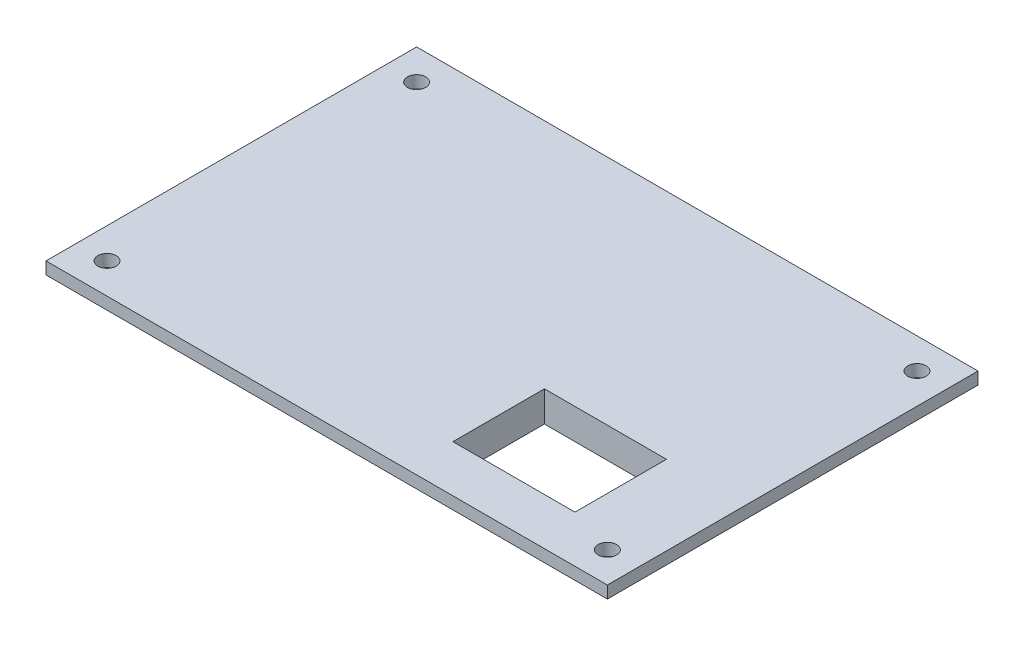
SolidWorks part; units mm, degrees
ref_plane "Спереди" through (0, 0, 0) normal (0, 0, 1) x (1, 0, 0)
ref_plane "Сверху" through (0, 0, 0) normal (0, 1, 0) x (1, 0, 0)
ref_plane "Справа" through (0, 0, 0) normal (1, 0, 0) x (0, 0, -1)
sketch "Эскиз1" plane through (0, 0, 0) normal (0, 1, 0) x (1, 0, 0)
  line L0 (-1000, 0) -> (49000, 0) construction
  line L1 (0, -1000) -> (0, 49000) construction
  line L2 (46, -1000) -> (46, 49000) construction
  line L3 (-46, -1000) -> (-46, 49000) construction
  line L4 (-1000, -30.37) -> (49000, -30.37) construction
  line L5 (-1000, 30.37) -> (49000, 30.37) construction
  line L6 (-46, 30.37) -> (-46, -30.37)
  line L7 (-46, -30.37) -> (46, -30.37)
  line L8 (46, -30.37) -> (46, 30.37)
  line L9 (46, 30.37) -> (-46, 30.37)
extrude "Бобышка-Вытянуть1" add sketch "Эскиз1" along normal blind 2
sketch "Эскиз2" plane through (0, 2, 0) normal (0, 1, 0) x (1, 0, 0)
  line L0 (-1000, 0) -> (49000, 0) construction
  line L1 (-41, -990.8865) -> (-41, 49009.1135) construction
  line L2 (41, -984.2014) -> (41, 49015.7986) construction
  line L3 (-1044.1748, 25.37) -> (48955.8252, 25.37) construction
  line L4 (42.5, -1000) -> (42.5, 49000) construction
  line L5 (-42.5, -1000) -> (-42.5, 49000) construction
  line L6 (-1038.32, -25.37) -> (48961.68, -25.37) construction
  line L7 (-1044.1748, 30.37) -> (48955.8252, 30.37) construction
  line L10 (-1038.32, -30.37) -> (48961.68, -30.37) construction
  line L12 (-46, -990.8865) -> (-46, 49009.1135) construction
  line L14 (46, -984.2014) -> (46, 49015.7986) construction
  circle A6 centre (-41, 25.37) radius 1.5
  circle A7 centre (41, 25.37) radius 1.5
  circle A8 centre (41, -25.37) radius 1.5
  circle A9 centre (-41, -25.37) radius 1.5
  dimension "D1" = 5
  dimension "D2" = 5
  dimension "D3" = 5
  dimension "D4" = 5
extrude "Вырез-Вытянуть1" cut sketch "Эскиз2" against normal blind 10
sketch "Эскиз3" plane through (0, 2, 0) normal (0, 1, 0) x (1, 0, 0)
  line L0 (-1033.1969, 30.37) -> (48966.8031, 30.37) construction
  line L2 (-1025.6477, -30.37) -> (48974.3523, -30.37) construction
  line L4 (-46, -985.3373) -> (-46, 49014.6627) construction
  line L6 (46, -986.4019) -> (46, 49013.5981) construction
  line L8 (0, -1000) -> (0, 49000) construction
  line L9 (-1000, 0) -> (49000, 0) construction
  line L14 (-1000, -15.185) -> (49000, -15.185) construction
  line L15 (23, -1000) -> (23, 49000) construction
  line L16 (33, -1000) -> (33, 49000) construction
  line L17 (13, -1000) -> (13, 49000) construction
  line L18 (76.37, 60.74) -> (-76.37, 60.74)
  line L19 (-76.37, 60.74) -> (-76.37, -60.74)
  line L20 (-76.37, -60.74) -> (76.37, -60.74)
  line L21 (76.37, -60.74) -> (76.37, 60.74)
  line L22 (76.37, 60.74) -> (-76.37, 60.74)
  line L23 (-76.37, 60.74) -> (-76.37, -60.74)
  line L24 (-76.37, -60.74) -> (76.37, -60.74)
  line L25 (76.37, -60.74) -> (76.37, 60.74)
  line L26 (-1000, -22.685) -> (49000, -22.685) construction
  line L27 (-1000, -7.685) -> (49000, -7.685) construction
  line L28 (13, -7.685) -> (13, -22.685)
  line L29 (13, -22.685) -> (33, -22.685)
  line L30 (33, -22.685) -> (33, -7.685)
  line L31 (33, -7.685) -> (13, -7.685)
  point P9 (23974.3523, -30.37)
  dimension "D1" = 30.37
extrude "Вырез-Вытянуть2" cut sketch "Эскиз3" against normal blind 10 contours L30 L31 L28 L29
sketch "Эскиз4" plane through (0, 0, 0) normal (0, -1, 0) x (1, 0, 0)
  line L0 (13, 22.685) -> (13, 7.685)
  line L1 (13, 7.685) -> (33, 7.685)
  line L2 (33, 7.685) -> (33, 22.685)
  line L3 (33, 22.685) -> (13, 22.685)
  line L4 (11, 24.685) -> (11, 5.685)
  line L5 (11, 5.685) -> (35, 5.685)
  line L6 (35, 5.685) -> (35, 24.685)
  line L7 (35, 24.685) -> (11, 24.685)
  dimension "D1" = 2
extrude "Бобышка-Вытянуть2" add sketch "Эскиз4" along normal blind 3
